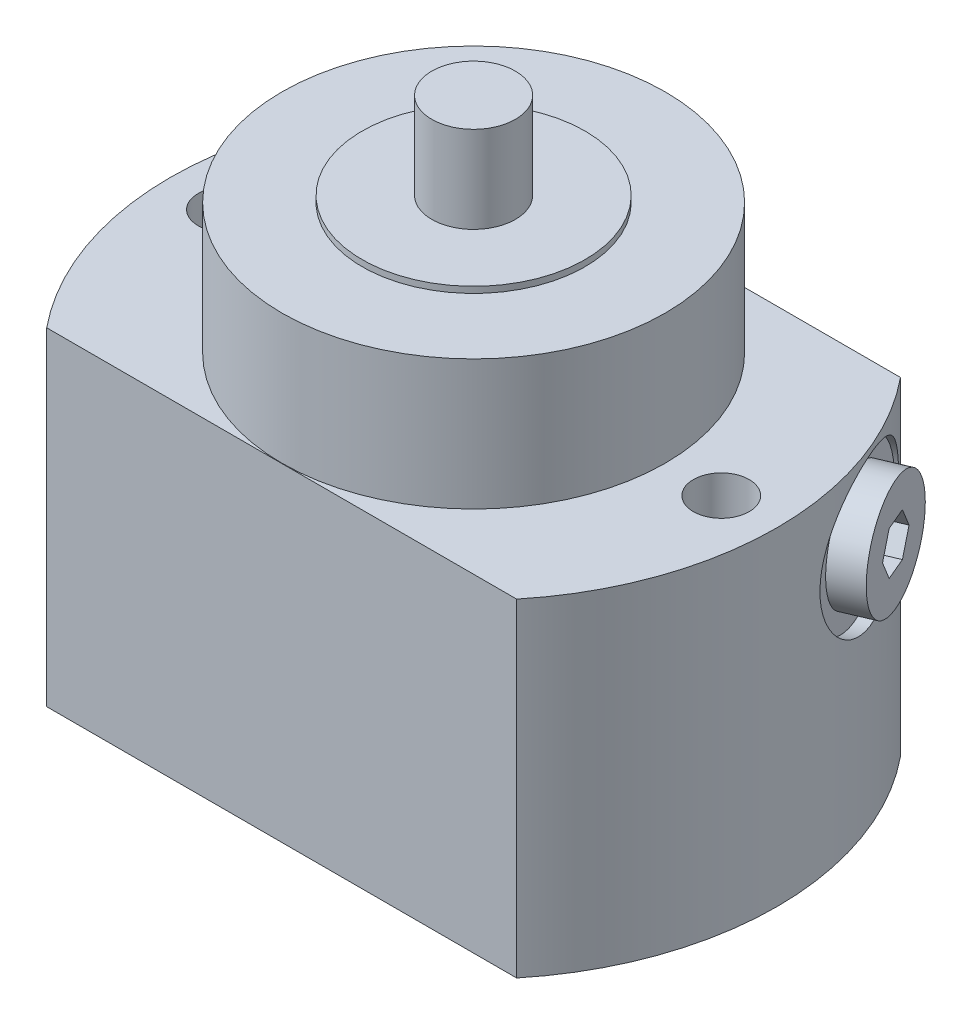
SolidWorks part; units mm, degrees
material "Alloy Steel"
ref_plane "Front Plane" through (0, 0, 0) normal (0, 0, 1) x (1, 0, 0)
ref_plane "Top Plane" through (0, 0, 0) normal (0, 1, 0) x (1, 0, 0)
ref_plane "Right Plane" through (0, 0, 0) normal (1, 0, 0) x (0, 0, -1)
sketch "Sketch1" plane through (0, 0, 0) normal (0, 1, 0) x (1, 0, 0)
  line L0 (-37.9473, 31) -> (37.9473, 31)
  line L1 (0, 0) -> (70.7148, 0) construction
  line L2 (-37.9473, -31) -> (37.9473, -31)
  arc A0 (-37.9473, 31) -> (-37.9473, -31) centre (0, 0) ccw
  arc A1 (37.9473, -31) -> (37.9473, 31) centre (0, 0) ccw
  dimension "D1" = 49
  dimension "D2" = 62
extrude "Extrude1" add sketch "Sketch1" along normal blind 53
sketch "Sketch2" plane through (0, 0, 0) normal (0, 0, 1) x (1, 0, 0)
  line L0 (0, 0) -> (0, 90.1953) construction
  line L1 (0, 89) -> (-6.75, 89)
  line L2 (-6.75, 89) -> (-6.75, 75)
  line L3 (-6.75, 75) -> (-18, 75)
  line L4 (-18, 75) -> (-18, 74)
  line L5 (-18, 74) -> (-30.95, 74)
  line L6 (-30.95, 74) -> (-30.95, 53)
  line L7 (-37.9473, 53) -> (37.9473, 53) construction
  line L8 (-30.95, 53) -> (0, 53)
  line L9 (0, 53) -> (0, 89)
  line L10 (-37.9473, 0) -> (37.9473, 0) construction
  dimension "D1" = 13.5
  dimension "D2" = 14
  dimension "D3" = 75
  dimension "D4" = 1
  dimension "D5" = 36
  dimension "D6" = 61.9
revolve "Revolve1" add sketch "Sketch2" angle 360 about L0
hole_wizard "Hole1" positions "Sketch4" profile "Sketch3" legacy end condition up to next
sketch "Sketch4" plane through (0, 53, 0) normal (0, 1, 0) x (-1, 0, 0)
  line L0 (0, 0) -> (0, 47.5777) construction
  point P0 (40, 0)
  point P7 (-40, 0)
  dimension "D1" = 80
sketch "Sketch3" plane through (-40, 53, 0) normal (1, 0, 0) x (0, 0, 1)
  line L0 (0, 0) -> (0, 53)
  line L1 (0, 53) -> (4.5, 53)
  line L2 (4.5, 53) -> (4.5, 0)
  line L3 (4.5, 0) -> (0, 0)
  line L4 (0, 110) -> (0, -10) construction
  dimension "Diameter" = 9
  dimension "Depth" = 53
sketch "Sketch5" plane through (0, 0, 0) normal (0, -1, 0) x (1, 0, 0)
  circle A0 centre (0, 0) radius 4
  dimension "D1" = 8
extrude "Cut-Extrude1" cut sketch "Sketch5" against normal blind 4
sketch "Sketch6" plane through (0, 0, 0) normal (0, -1, 0) x (1, 0, 0)
  circle A0 centre (31, -13) radius 5.5
  dimension "D3" = 11
  dimension "D1" = 31
  dimension "D2" = 13
extrude "Cut-Extrude2" cut sketch "Sketch6" against normal blind 3
sketch "Sketch7" plane through (0, 3, 0) normal (0, -1, 0) x (1, 0, 0)
  circle A0 centre (31, -13) radius 2
  dimension "D1" = 4
extrude "Cut-Extrude3" cut sketch "Sketch7" against normal blind 33
ref_plane "Plane1" through (0, 0, 0) normal (0.3907, 0, 0.9205) x (0.9205, 0, -0.3907)
sketch "Sketch8" plane through (0, 0, 0) normal (0.3907, 0, 0.9205) x (0.9205, 0, -0.3907)
  line L0 (51.5856, 40) -> (-19.0781, 40) construction
  line L1 (-47.0434, 0) -> (22.818, 0) construction
  line L2 (49, 28) -> (47, 28)
  line L3 (49, 0) -> (49, 53) construction
  line L4 (47, 28) -> (47, 33.4215)
  line L5 (47, 33.4215) -> (45.5174, 34.2775)
  line L6 (45.5174, 34.2775) -> (32, 34.2775)
  line L7 (32, 34.2775) -> (32, 40)
  line L8 (32, 40) -> (49, 40)
  line L9 (49, 40) -> (49, 28)
  dimension "D1" = 40
  dimension "D2" = 2
  dimension "D3" = 15
  dimension "D4" = 11.445
  dimension "D5" = 24
  dimension "D6" = 30
  dimension "D7" = 13.157
revolve "Cut-Revolve1" cut sketch "Sketch8" angle 360 about L0
sketch "Sketch9" plane through (0, 0, 0) normal (0.3907, 0, 0.9205) x (0.9205, 0, -0.3907)
  line L0 (58.5879, 40) -> (15.4121, 40) construction
  line L1 (32, 40) -> (45.5174, 40) construction
  line L2 (47, 28) -> (47, 52) construction
  line L3 (35.6098, 34.2775) -> (45.5174, 34.2775) construction
  line L4 (47, 31) -> (47, 34.2775)
  line L5 (38, 34.2775) -> (47, 34.2775)
  line L6 (47, 31) -> (52, 31)
  line L7 (52, 31) -> (52, 40)
  line L8 (52, 40) -> (37, 40)
  line L9 (37, 40) -> (37, 35.2775)
  line L10 (37, 35.2775) -> (38, 34.2775)
  dimension "D1" = 45
  dimension "D2" = 4.7225
  dimension "D3" = 10
  dimension "D4" = 5
  dimension "D5" = 18
revolve "Revolve2" add sketch "Sketch9" angle 360 about L0
sketch "Sketch10" plane through (47.8663, 0, -20.318) normal (0.9205, 0, -0.3907) x (-0.3907, 0, -0.9205)
  line L1 (4.0415, 40) -> (2.0207, 43.5)
  line L2 (2.0207, 43.5) -> (-2.0207, 43.5)
  line L3 (-2.0207, 43.5) -> (-4.0415, 40)
  line L4 (-4.0415, 40) -> (-2.0207, 36.5)
  line L5 (-2.0207, 36.5) -> (2.0207, 36.5)
  line L6 (2.0207, 36.5) -> (4.0415, 40)
  circle A0 centre (0, 40) radius 3.5 construction
  circle A1 centre (0, 40) radius 9 construction
  dimension "D1" = 7
extrude "Cut-Extrude4" cut sketch "Sketch10" against normal blind 5
